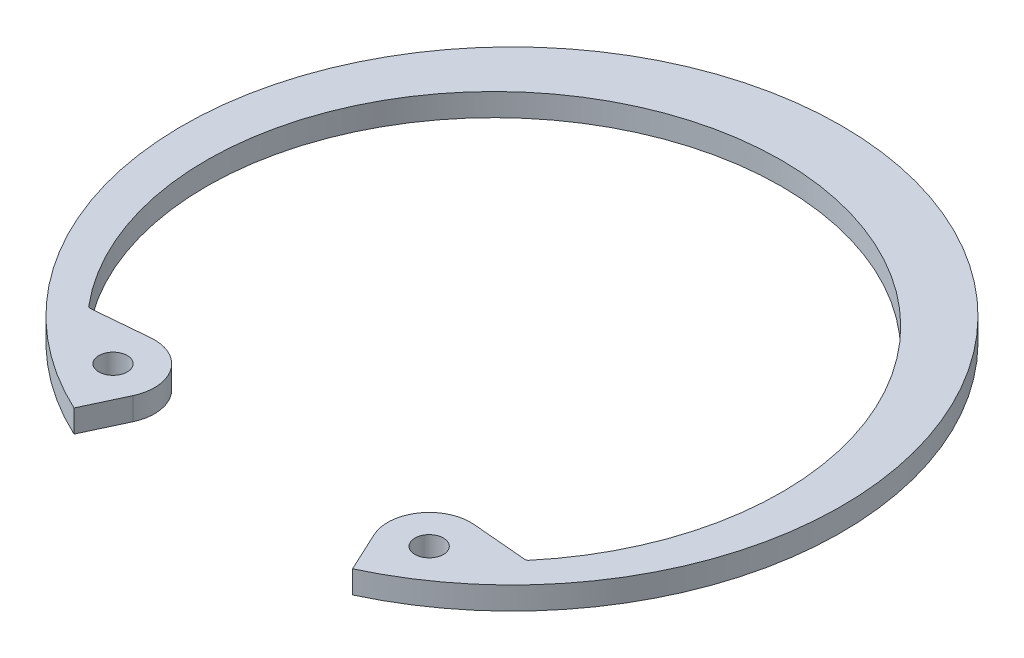
SolidWorks part; units mm, degrees
material "Cast Carbon Steel"
ref_plane "Front" through (0, 0, 0) normal (0, 0, 1) x (1, 0, 0)
ref_plane "Top" through (0, 0, 0) normal (0, 1, 0) x (1, 0, 0)
ref_plane "Right" through (0, 0, 0) normal (1, 0, 0) x (0, 0, -1)
sketch "Sketch2" plane through (0, 0, 0) normal (0, 1, 0) x (1, 0, 0)
  line L0 (0, 0) -> (0, -22.9108) construction
  line L1 (-15.2182, -14.2202) -> (-16.74, -15.6422) construction
  line L2 (9.6825, -20.7642) -> (8.376, -17.9624)
  line L3 (-9.6825, -20.7642) -> (-8.376, -17.9624)
  line L4 (0, 18.7452) -> (0, 22.9108) construction
  line L5 (15.2182, -14.2202) -> (11.2401, -13.8721)
  line L6 (-15.2182, -14.2202) -> (-11.2401, -13.8721)
  line L7 (9.407, -14.3338) -> (-1.08, -21.2163) construction
  line L8 (-1.08, -21.2163) -> (2.0835, -26.0367) construction
  line L9 (2.0835, -26.0367) -> (12.5706, -19.1543) construction
  line L10 (9.407, -14.3338) -> (12.5706, -19.1543) construction
  line L11 (10.9888, -16.744) -> (8.376, -17.9624) construction
  line L12 (10.9888, -16.744) -> (12.5706, -19.1543) construction
  line L13 (9.407, -14.3338) -> (-9.407, -14.3338) construction
  line L14 (-9.407, -14.3338) -> (-12.5706, -19.1543) construction
  line L15 (-22.9108, 0) -> (22.9108, 0) construction
  arc A1 (9.6825, -20.7642) -> (-9.6825, -20.7642) centre (0, 0) ccw
  arc A2 (15.2182, -14.2202) -> (-15.2182, -14.2202) centre (0, -1.2501) ccw
  circle A3 centre (0, 0) radius 22.9108 construction
  arc A4 (8.376, -17.9624) -> (11.2401, -13.8721) centre (10.9888, -16.744) cw
  arc A5 (-8.376, -17.9624) -> (-11.2401, -13.8721) centre (-10.9888, -16.744) ccw
  circle A6 centre (10.9888, -16.744) radius 0.9906
  circle A7 centre (-10.9888, -16.744) radius 0.9906
  arc A8 (15.2182, -14.2202) -> (-15.2182, -14.2202) centre (0, -1.2501) cw construction
  circle A9 centre (0, 0) radius 15.24 construction
  point P5 (10.9888, -16.744)
  point P10 (9.407, -14.3338)
  dimension "D1" = 60
  dimension "D2" = 60
  dimension "L" = 30.48
  dimension "R" = 1.9812
  dimension "Df" = 45.8216
  dimension "H" = 5.7658
  dimension "Angle" = 25
  dimension "Sec. Max" = 4.1656
  dimension "Sec. Min" = 2.0828
extrude "Extrude1" add sketch "Sketch2" against normal blind 1.5748
fillet "Fillet1" radius 0.254 2 edges at (-15.2182, -0.7874, 14.2202) (15.2182, -0.7874, 14.2202)
sketch "Sketch3" plane through (0, 0, 0) normal (1, 0, 0) x (0, 0, -1)
  line L0 (-20.6375, -16.4592) -> (-20.6375, -1.651)
  line L1 (-20.6375, -1.651) -> (-21.9075, -1.651)
  line L2 (-21.9075, -1.651) -> (-21.9075, 0.0762)
  line L3 (-21.9075, 0.0762) -> (-20.6375, 0.0762)
  line L4 (-20.6375, 0.0762) -> (-20.6375, 2.4384)
  line L5 (-20.6375, -16.4592) -> (-23.1775, -16.4592)
  line L6 (-20.6375, -1.651) -> (0, -1.651) construction
  line L7 (-20.6375, 2.4384) -> (-23.1775, 2.4384)
  line L8 (0, 130.3401) -> (0, 164.6301) construction
  line L9 (0, -1.651) -> (0, 0.0762) construction
  line L10 (0, 0.0762) -> (-20.6375, 0.0762) construction
  line L11 (-21.9075, -0.7874) -> (0, -0.7874) construction
  line L12 (0, -135.0899) -> (0, 130.3401) construction
  line L13 (-14.1191, -1.5748) -> (18.7452, -1.5748) construction
  line L14 (-23.1775, -16.4592) -> (-23.1775, 2.4384)
  dimension "D1" = 0.7874
  dimension "Shaft Lg" = 18.8976
  dimension "Dg" = 43.815
  dimension "Db" = 41.275
  dimension "W" = 1.7272
  dimension "D2" = 1.27
  dimension "D3" = 2.3622
  dimension "D4" = 1.27
revolve "Revolve1" [suppressed] add sketch "Sketch3" angle 360 about L8
delete or keep bodies "Body-Delete1" [suppressed] type delete bodies bodies 116
equation "\"D3@Sketch3\" = \"Shaft Lg@Sketch3\"/8"
equation "\"Shaft Lg@Sketch3\" = \"D1@Extrude1\"*12"
equation "\"D1@Sketch3\" = \"D1@Extrude1\"/2"
equation "\"D2@Sketch3\" = \"D4@Sketch3\""
